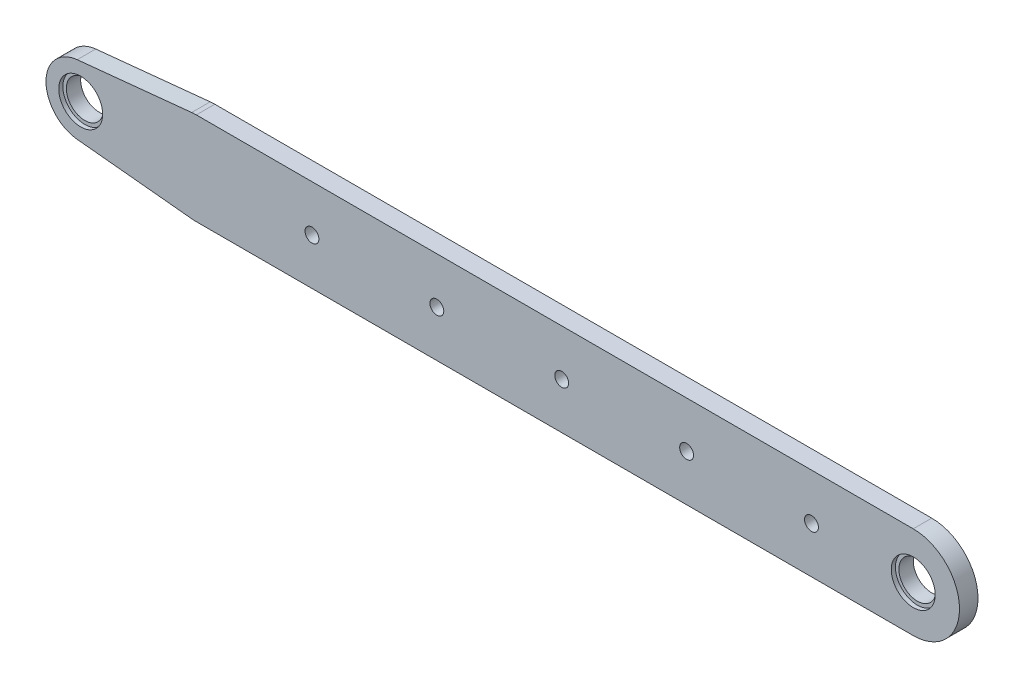
SolidWorks part; units mm, degrees
ref_plane "前视基准面" through (0, 0, 0) normal (0, 0, 1) x (1, 0, 0)
ref_plane "上视基准面" through (0, 0, 0) normal (0, 1, 0) x (1, 0, 0)
ref_plane "右视基准面" through (0, 0, 0) normal (1, 0, 0) x (0, 0, -1)
other "Configuration Table"
sketch "草图1" plane through (0, 0, 0) normal (0, 0, 1) x (1, 0, 0)
  line L0 (-77.5, 0) -> (77.5, 0) construction
  line L1 (-77.5, 10) -> (77.5, 10)
  line L2 (-77.5, -10) -> (77.5, -10)
  line L3 (-77.5, 0) -> (-211.495, 0) construction
  line L4 (-103.25, 7.4624) -> (-78.5, 9.9499)
  line L5 (-103.25, -7.4624) -> (-78.5, -9.9499)
  arc A0 (-77.5, 10) -> (-77.5, -10) centre (-77.5, 0) ccw
  arc A1 (77.5, -10) -> (77.5, 10) centre (77.5, 0) ccw
  circle A2 centre (-77.5, 0) radius 10
  arc A3 (-103.25, 7.4624) -> (-103.25, -7.4624) centre (-102.5, 0) ccw
  circle A4 centre (77.5, 0) radius 4 construction
  circle A5 centre (-102.5, 0) radius 4 construction
  point P3 (0, 0)
  dimension "D1" = 10
  dimension "D4" = 7.5
  dimension "D5" = 8
  dimension "D6" = 8
  dimension "D2" = 180
  dimension "D3" = 25
extrude "凸台-拉伸1" add sketch "草图1" along normal blind 4 contours A2 L2 A1 L1 | A0 A2 | L4 A3 L5 A0
sketch "草图2" plane through (0, 0, 4) normal (0, 0, 1) x (1, 0, 0)
  line L8 (77.5, 10) -> (-77.5, 10)
  line L9 (-78.5, 9.9499) -> (-103.25, 7.4624)
  line L10 (-103.25, -7.4624) -> (-78.5, -9.9499)
  line L11 (-77.5, -10) -> (77.5, -10)
  line L12 (77.5, 10) -> (-77.5, 10)
  line L13 (-78.5, 9.9499) -> (-103.25, 7.4624)
  line L14 (-103.25, -7.4624) -> (-78.5, -9.9499)
  line L15 (-77.5, -10) -> (77.5, -10)
  arc A8 (-77.5, 10) -> (-78.5, 9.9499) centre (-77.5, 0) ccw
  arc A9 (-103.25, 7.4624) -> (-103.25, -7.4624) centre (-102.5, 0) ccw
  arc A10 (-78.5, -9.9499) -> (-77.5, -10) centre (-77.5, 0) ccw
  arc A11 (77.5, -10) -> (77.5, 10) centre (77.5, 0) ccw
  arc A12 (-77.5, 10) -> (-78.5, 9.9499) centre (-77.5, 0) ccw
  arc A13 (-103.25, 7.4624) -> (-103.25, -7.4624) centre (-102.5, 0) ccw
  arc A14 (-78.5, -9.9499) -> (-77.5, -10) centre (-77.5, 0) ccw
  arc A15 (77.5, -10) -> (77.5, 10) centre (77.5, 0) ccw
  dimension "D1" = 0
sketch "草图7" plane through (0, 0, 4) normal (0, 0, 1) x (1, 0, 0)
  point P0 (-102.5, 0)
  point P3 (77.5, 0)
hole_wizard "M5 六角头螺栓的柱形沉头孔1" positions "草图7" profile "草图8" counterbore size "M5" standard "GB" end condition through all
sketch "草图8" plane through (-102.5, 0, 4) normal (1, 0, 0) x (0, -1, 0)
  line L0 (0, 0) -> (0, 4)
  line L1 (0, 4) -> (4, 4)
  line L3 (4, 4) -> (4, 0.9)
  line L4 (4, 0.9) -> (4.75, 0.9)
  line L5 (4.75, 0.9) -> (4.75, 0)
  line L7 (4.75, 0) -> (0, 0)
  line L11 (0, -6.35) -> (0, 107.95) construction
  dimension "通孔孔直径" = 8
  dimension "通孔孔深度" = 4
  dimension "柱形沉头孔直径" = 9.5
  dimension "柱形沉头孔深度" = 0.9
sketch "草图11" plane through (0, 0, 4) normal (0, 0, 1) x (1, 0, 0)
  line L0 (-102.5, 0) -> (77.5, 0) construction
  circle A0 centre (-52.5, 0) radius 1.5
  circle A1 centre (-25.5, 0) radius 1.5
  circle A2 centre (1.5, 0) radius 1.5
  circle A3 centre (28.5, 0) radius 1.5
  circle A4 centre (55.5, 0) radius 1.5
  dimension "D2" = 3
  dimension "D1" = 50
  dimension "D4" = 27
  dimension "D3" = 5
extrude "切除-拉伸1" cut sketch "草图11" against normal through all both and the other way through all
equation "\"BigArm\"= 180mm"
